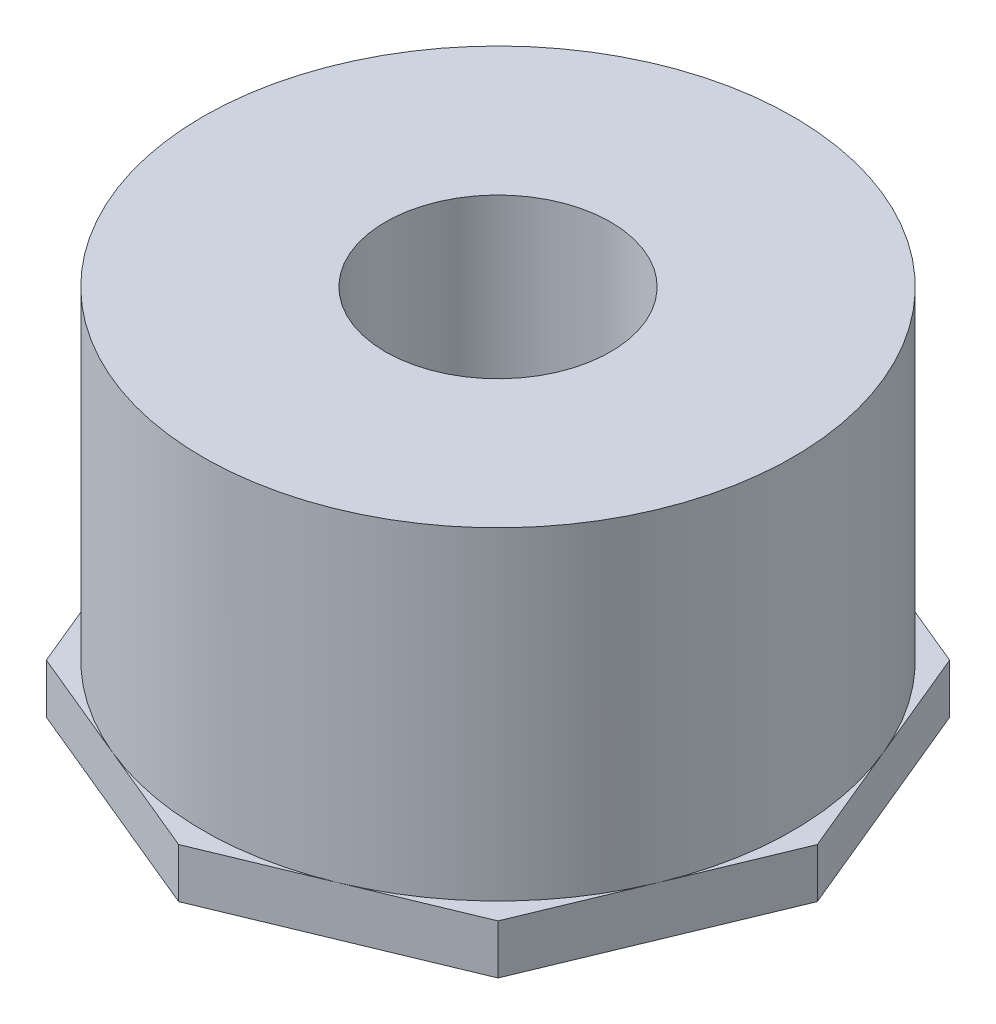
SolidWorks part; units mm, degrees
ref_plane "Front" through (0, 0, 0) normal (0, 0, 1) x (1, 0, 0)
ref_plane "Top" through (0, 0, 0) normal (0, 1, 0) x (1, 0, 0)
ref_plane "Right" through (0, 0, 0) normal (1, 0, 0) x (0, 0, -1)
sketch "Sketch1" plane through (0, 0, 0) normal (0, 0, 1) x (1, 0, 0)
  line L0 (0, 0) -> (0, 38.1)
  line L1 (0, 38.1) -> (-30.1625, 38.1)
  line L2 (-30.1625, 38.1) -> (-30.1625, 0)
  line L5 (-30.1625, 0) -> (0, 0)
  line L6 (0, 0) -> (0, -9.8334) construction
  dimension "D1" = 60.325
  dimension "D3" = 38.1
revolve "Revolve1" add sketch "Sketch1" angle 360 about L6
sketch "Sketch2" plane through (0, 0, 0) normal (0, -1, 0) x (1, 0, 0)
  line L1 (0, 32.6477) -> (-23.0854, 23.0854)
  line L2 (-23.0854, 23.0854) -> (-32.6477, 0)
  line L3 (-32.6477, 0) -> (-23.0854, -23.0854)
  line L4 (-23.0854, -23.0854) -> (0, -32.6477)
  line L5 (0, -32.6477) -> (23.0854, -23.0854)
  line L6 (23.0854, -23.0854) -> (32.6477, 0)
  line L7 (32.6477, 0) -> (23.0854, 23.0854)
  line L8 (23.0854, 23.0854) -> (0, 32.6477)
  circle A0 centre (0, 0) radius 30.1625 construction
  circle A1 centre (0, 0) radius 30.1625 construction
extrude "Boss-Extrude1" add sketch "Sketch2" against normal blind 5.0546
hole_wizard "3/4 NPT Tapped Hole1" positions "Sketch3" profile "Sketch4" size "3/4" standard "ANSI Inch" end condition through all
sketch "Sketch3" plane through (0, 0, 0) normal (0, -1, 0) x (-1, 0, 0)
  point P3 (0, 0)
sketch "Sketch4" plane through (0, 0, 0) normal (1, 0, 0) x (0, 0, -1)
  line L0 (0, 0) -> (0, 38.1)
  line L1 (0, 38.1) -> (11.5062, 38.1)
  line L2 (-12.1379, 14.0538) -> (-12.5586, 0) construction
  line L3 (11.5062, 38.1) -> (11.5062, 14.0538)
  line L4 (11.5062, 14.0538) -> (12.1379, 14.0538)
  line L5 (12.1379, 14.0538) -> (12.5586, 0)
  line L7 (12.5586, 0) -> (0, 0)
  line L8 (0, -6.35) -> (0, 107.95) construction
  line L11 (-11.5062, 14.0538) -> (-12.1379, 14.0538) construction
  dimension "Thru Tap Drill Dia." = 23.0124
  dimension "Thru Tap Drill Depth" = 38.1
  dimension "Thread Dia." = 25.1173
  dimension "Thread Angle" = 3.43
  dimension "Thread Depth" = 14.0538
cosmetic thread "Hole Thread1" parameters "D1"=14.0538, "D2"=26.67
